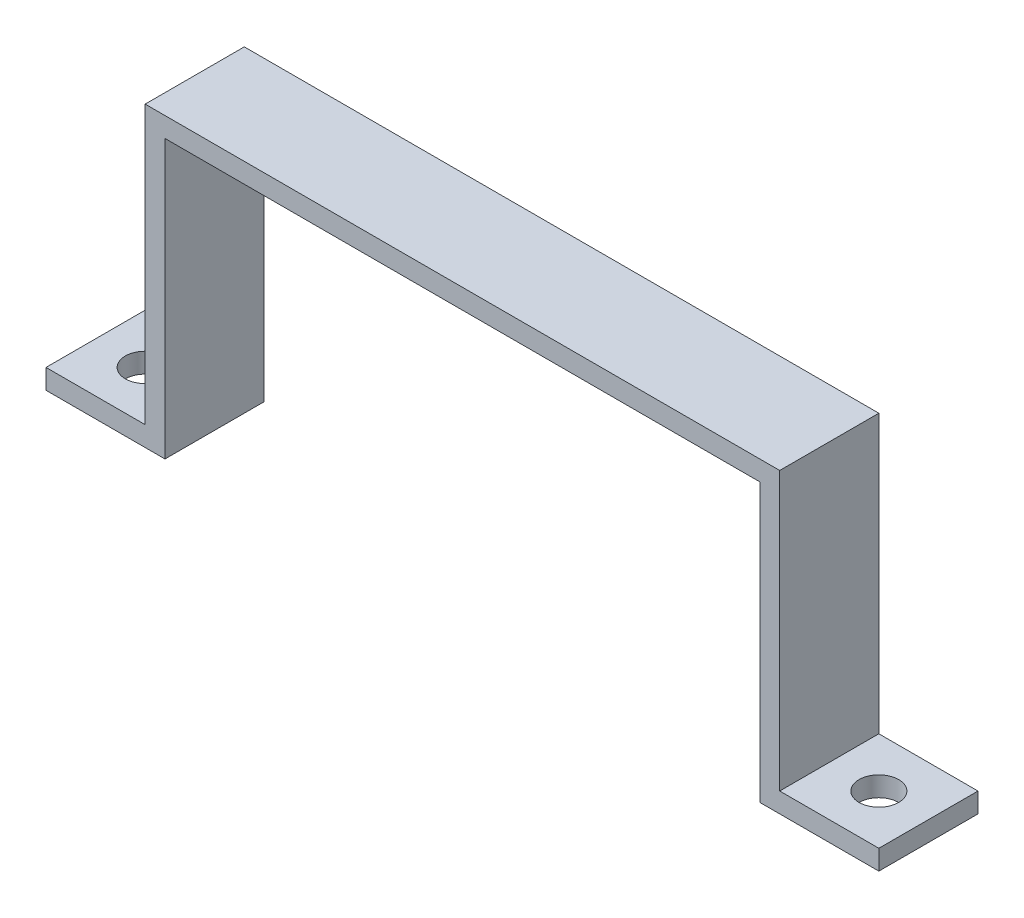
SolidWorks part; units mm, degrees
material "ABS"
ref_plane "Front Plane" through (0, 0, 0) normal (0, 0, 1) x (1, 0, 0)
ref_plane "Top Plane" through (0, 0, 0) normal (0, 1, 0) x (1, 0, 0)
ref_plane "Right Plane" through (0, 0, 0) normal (1, 0, 0) x (0, 0, -1)
sketch "Sketch1" plane through (0, 0, 0) normal (0, 0, 1) x (1, 0, 0)
  line L1 (-57.4285, -21.3533) -> (-37.4285, -21.3533)
  line L2 (-57.4285, -21.3533) -> (-57.4285, -19.3533)
  line L3 (-57.4285, -19.3533) -> (-37.4285, -19.3533)
  line L5 (-37.4285, -21.3533) -> (-35.4285, -21.3533)
  line L6 (-37.4285, -19.3533) -> (-37.4285, 8.6467)
  line L7 (-37.4285, 8.6467) -> (-35.4285, 8.6467)
  line L8 (-35.4285, -21.3533) -> (-35.4285, 6.6467)
  line L9 (-35.4285, 8.6467) -> (24.5715, 8.6467)
  line L11 (-35.4285, 6.6467) -> (24.5715, 6.6467)
  line L13 (24.5715, 8.6467) -> (26.5715, 8.6467)
  line L14 (24.5715, 6.6467) -> (24.5715, -21.3533)
  line L15 (24.5715, -21.3533) -> (26.5715, -21.3533)
  line L16 (26.5715, 8.6467) -> (26.5715, -19.3533)
  line L17 (26.5715, -21.3533) -> (46.5715, -21.3533)
  line L19 (26.5715, -19.3533) -> (46.5715, -19.3533)
  line L20 (46.5715, -21.3533) -> (46.5715, -19.3533)
  dimension "D1" = 2
  dimension "D2" = 2
  dimension "D3" = 2
  dimension "D4" = 2
  dimension "D5" = 2
  dimension "D6" = 60
  dimension "D7" = 30
  dimension "D8" = 30
  dimension "D9" = 20
  dimension "D10" = 20
extrude "Boss-Extrude1" add sketch "Sketch1" along normal blind 10
sketch "Sketch2" plane through (0, -19.3533, 0) normal (0, 1, 0) x (1, 0, 0)
  line L0 (-37.4285, -10) -> (-37.4285, 0) construction
  line L1 (26.5715, -10) -> (26.5715, 0) construction
  line L2 (-37.4285, -10) -> (-57.4285, -10) construction
  line L3 (46.5715, -10) -> (26.5715, -10) construction
  circle A0 centre (-42.4285, -5) radius 2
  circle A1 centre (31.5715, -5) radius 2
  dimension "D1" = 4
  dimension "D4" = 4
  dimension "D2" = 5
  dimension "D3" = 5
  dimension "D5" = 5
  dimension "D6" = 5
extrude "Cut-Extrude2" cut sketch "Sketch2" against normal blind 10
sketch "Sketch3" plane through (0, -19.3533, 0) normal (0, 1, 0) x (1, 0, 0)
  line L0 (-37.4285, -10) -> (-57.4285, -10) construction
  line L1 (-57.4285, 0) -> (-47.4285, 0)
  line L2 (-57.4285, 0) -> (-57.4285, -10)
  line L3 (-57.4285, -10) -> (-47.4285, -10)
  line L4 (-47.4285, 0) -> (-47.4285, -10)
  line L5 (46.5715, -10) -> (26.5715, -10) construction
  line L6 (46.5715, 0) -> (36.5715, 0)
  line L7 (46.5715, 0) -> (46.5715, -10)
  line L8 (46.5715, -10) -> (36.5715, -10)
  line L9 (36.5715, 0) -> (36.5715, -10)
extrude "Cut-Extrude3" cut sketch "Sketch3" against normal blind 10
